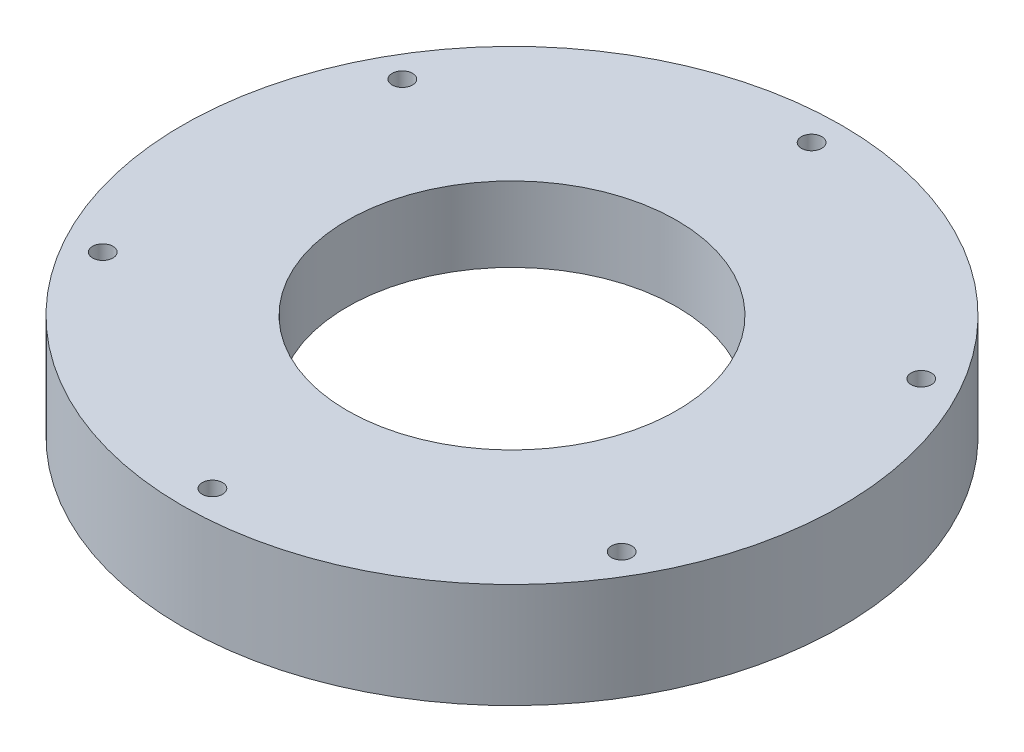
SolidWorks part; units mm, degrees
ref_plane "Front Plane" through (0, 0, 0) normal (0, 0, 1) x (1, 0, 0)
ref_plane "Top Plane" through (0, 0, 0) normal (0, 1, 0) x (1, 0, 0)
ref_plane "Right Plane" through (0, 0, 0) normal (1, 0, 0) x (0, 0, -1)
sketch "Sketch1" plane through (0, 0, 0) normal (0, 1, 0) x (1, 0, 0)
  line L1 (0, 0) -> (0, 100) construction
  circle A0 centre (0, 0) radius 55
  circle A1 centre (0, 0) radius 110
  circle A2 centre (0, 100) radius 3.4
  circle A8 centre (0, 0) radius 80 construction
  circle A9 centre (0, 0) radius 100 construction
  circle A12 centre (86.6025, 50) radius 3.4
  circle A13 centre (86.6025, -50) radius 3.4
  circle A14 centre (0, -100) radius 3.4
  circle A15 centre (-86.6025, -50) radius 3.4
  circle A16 centre (-86.6025, 50) radius 3.4
  point P19 (4.3301, 2.5)
  point P25 (0, 0)
  point P27 (0, 0)
  dimension "D1" = 110
  dimension "D2" = 220
  dimension "D3" = 6.8
  dimension "D5" = 160
  dimension "D9" = 200
  dimension "D4" = 100
  dimension "D10" = 6
extrude "Boss-Extrude1" add sketch "Sketch1" along normal blind 35
sketch "Sketch2" plane through (0, 0, 0) normal (0, -1, 0) x (1, 0, 0)
  circle A0 centre (0, 0) radius 87.5
  dimension "D1" = 175
extrude "Cut-Extrude1" cut sketch "Sketch2" against normal blind 10
